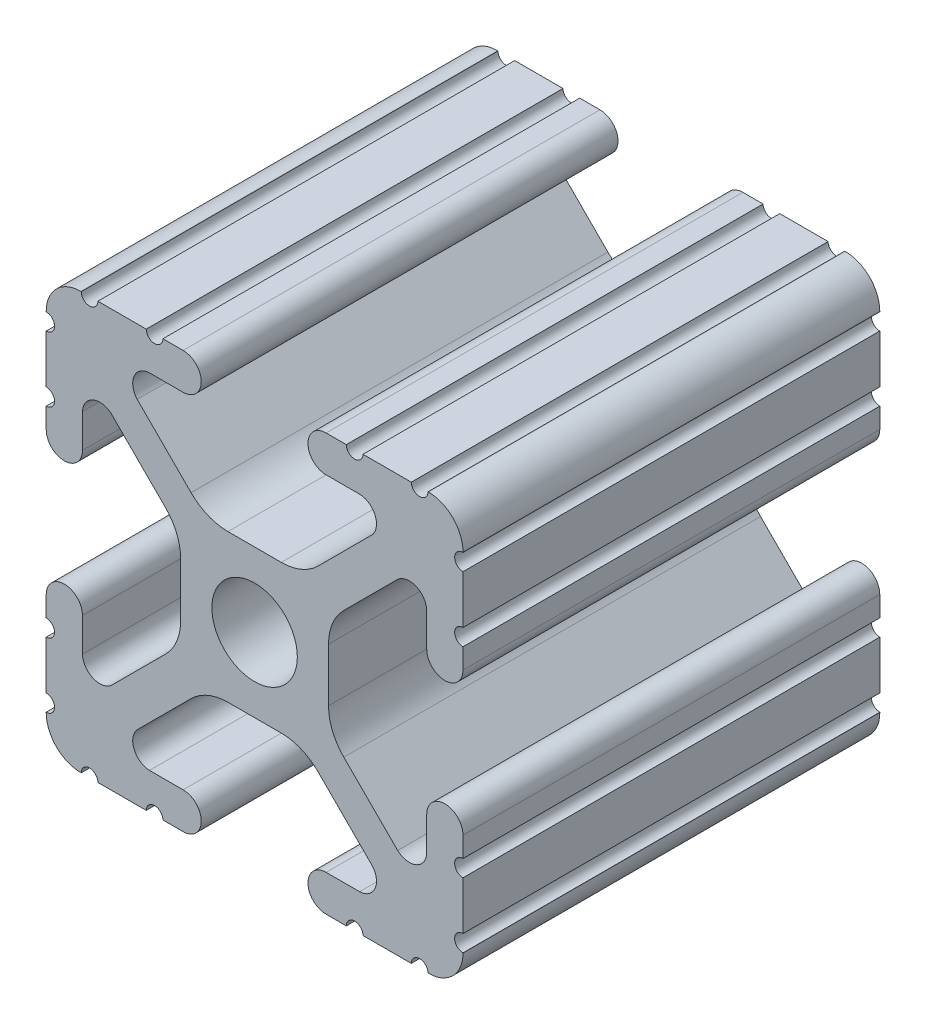
SolidWorks part; units mm, degrees
ref_plane "Front Plane" through (0, 0, 0) normal (0, 0, 1) x (1, 0, 0)
ref_plane "Top Plane" through (0, 0, 0) normal (0, 1, 0) x (1, 0, 0)
ref_plane "Right Plane" through (0, 0, 0) normal (1, 0, 0) x (0, 0, -1)
sketch "Sketch1" plane through (0, 0, 0) normal (0, 0, 1) x (1, 0, 0)
  line L0 (813.039, 579.2904) -> (813.039, 582.2368)
  line L1 (813.039, 583.2528) -> (813.039, 584.4847)
  line L2 (810.8292, 584.4847) -> (810.8292, 582.4359)
  line L3 (809.0573, 581.6856) -> (805.7733, 584.9696)
  line L4 (804.8434, 587.2147) -> (804.8434, 590.4671)
  line L5 (805.7733, 592.7122) -> (809.0571, 595.9959)
  line L6 (810.8292, 595.2394) -> (810.8292, 593.1969)
  line L7 (813.039, 593.1969) -> (813.039, 594.4288)
  line L8 (813.039, 595.4448) -> (813.039, 598.3912)
  line L9 (813.039, 599.4072) -> (813.039, 599.4326)
  line L10 (810.9308, 601.5408) -> (810.9054, 601.5408)
  line L11 (809.8894, 601.5408) -> (806.943, 601.5408)
  line L12 (805.927, 601.5408) -> (804.6951, 601.5408)
  line L13 (804.6951, 599.331) -> (806.7439, 599.331)
  line L14 (807.4942, 597.5592) -> (804.2102, 594.2752)
  line L15 (801.9651, 593.3452) -> (798.7127, 593.3452)
  line L16 (796.4676, 594.2752) -> (793.1839, 597.559)
  line L17 (793.9404, 599.331) -> (795.9829, 599.331)
  line L18 (795.9829, 601.5408) -> (794.751, 601.5408)
  line L19 (793.735, 601.5408) -> (790.7886, 601.5408)
  line L20 (789.7726, 601.5408) -> (789.7472, 601.5408)
  line L21 (787.639, 599.4326) -> (787.639, 599.4072)
  line L22 (787.639, 598.3912) -> (787.639, 595.4448)
  line L23 (787.639, 594.4288) -> (787.639, 593.1969)
  line L24 (789.8488, 593.1969) -> (789.8488, 595.2458)
  line L25 (791.6206, 595.996) -> (794.9046, 592.7121)
  line L26 (795.8346, 590.467) -> (795.8346, 587.2146)
  line L27 (794.9046, 584.9695) -> (791.6208, 581.6858)
  line L28 (789.8488, 582.4423) -> (789.8488, 584.4847)
  line L29 (787.639, 584.4847) -> (787.639, 583.2528)
  line L30 (787.639, 582.2368) -> (787.639, 579.2904)
  line L31 (787.639, 578.2744) -> (787.639, 578.249)
  line L32 (789.7472, 576.1408) -> (789.7726, 576.1408)
  line L33 (790.7886, 576.1408) -> (793.735, 576.1408)
  line L34 (794.751, 576.1408) -> (795.9829, 576.1408)
  line L35 (795.9829, 578.3506) -> (793.934, 578.3506)
  line L36 (793.1838, 580.1225) -> (796.4677, 583.4065)
  line L37 (798.7128, 584.3364) -> (801.9652, 584.3364)
  line L38 (804.2103, 583.4065) -> (807.494, 580.1227)
  line L39 (806.7375, 578.3506) -> (804.6951, 578.3506)
  line L40 (804.6951, 576.1408) -> (805.927, 576.1408)
  line L41 (806.943, 576.1408) -> (809.8894, 576.1408)
  line L42 (810.9054, 576.1408) -> (810.9308, 576.1408)
  line L43 (813.039, 578.249) -> (813.039, 578.2744)
  circle A0 centre (800.339, 588.8408) radius 2.6035
  arc A1 (813.039, 579.2904) -> (813.039, 578.2744) centre (813.039, 578.7824) ccw
  arc A2 (813.039, 583.2528) -> (813.039, 582.2368) centre (813.039, 582.7448) ccw
  arc A3 (813.039, 584.4847) -> (810.8292, 584.4847) centre (811.9341, 584.4847) ccw
  arc A4 (809.0573, 581.6856) -> (810.8292, 582.4359) centre (809.7692, 582.4718) ccw
  arc A5 (804.8434, 587.2147) -> (805.7733, 584.9696) centre (808.0184, 587.2147) ccw
  arc A6 (805.7733, 592.7122) -> (804.8434, 590.4671) centre (808.0184, 590.4671) ccw
  arc A7 (810.8292, 595.2394) -> (809.0571, 595.9959) centre (809.769, 595.2098) ccw
  arc A8 (810.8292, 593.1969) -> (813.039, 593.1969) centre (811.9341, 593.1969) ccw
  arc A9 (813.039, 595.4448) -> (813.039, 594.4288) centre (813.039, 594.9368) ccw
  arc A10 (813.039, 599.4072) -> (813.039, 598.3912) centre (813.039, 598.8992) ccw
  arc A11 (813.039, 599.4326) -> (810.9308, 601.5408) centre (810.9308, 599.4326) ccw
  arc A12 (809.8894, 601.5408) -> (810.9054, 601.5408) centre (810.3974, 601.5408) ccw
  arc A13 (805.927, 601.5408) -> (806.943, 601.5408) centre (806.435, 601.5408) ccw
  arc A14 (804.6951, 601.5408) -> (804.6951, 599.331) centre (804.6951, 600.4359) ccw
  arc A15 (807.4942, 597.5592) -> (806.7439, 599.331) centre (806.708, 598.2711) ccw
  arc A16 (801.9651, 593.3452) -> (804.2102, 594.2752) centre (801.9651, 596.5202) ccw
  arc A17 (796.4676, 594.2752) -> (798.7127, 593.3452) centre (798.7127, 596.5202) ccw
  arc A18 (793.9404, 599.331) -> (793.1839, 597.559) centre (793.97, 598.2709) ccw
  arc A19 (795.9829, 599.331) -> (795.9829, 601.5408) centre (795.9829, 600.4359) ccw
  arc A20 (793.735, 601.5408) -> (794.751, 601.5408) centre (794.243, 601.5408) ccw
  arc A21 (789.7726, 601.5408) -> (790.7886, 601.5408) centre (790.2806, 601.5408) ccw
  arc A22 (789.7472, 601.5408) -> (787.639, 599.4326) centre (789.7472, 599.4326) ccw
  arc A23 (787.639, 598.3912) -> (787.639, 599.4072) centre (787.639, 598.8992) ccw
  arc A24 (787.639, 594.4288) -> (787.639, 595.4448) centre (787.639, 594.9368) ccw
  arc A25 (787.639, 593.1969) -> (789.8488, 593.1969) centre (788.7439, 593.1969) ccw
  arc A26 (791.6206, 595.996) -> (789.8488, 595.2458) centre (790.9087, 595.2099) ccw
  arc A27 (795.8346, 590.467) -> (794.9046, 592.7121) centre (792.6596, 590.467) ccw
  arc A28 (794.9046, 584.9695) -> (795.8346, 587.2146) centre (792.6596, 587.2146) ccw
  arc A29 (789.8488, 582.4423) -> (791.6208, 581.6858) centre (790.9089, 582.4719) ccw
  arc A30 (789.8488, 584.4847) -> (787.639, 584.4847) centre (788.7439, 584.4847) ccw
  arc A31 (787.639, 582.2368) -> (787.639, 583.2528) centre (787.639, 582.7448) ccw
  arc A32 (787.639, 578.2744) -> (787.639, 579.2904) centre (787.639, 578.7824) ccw
  arc A33 (787.639, 578.249) -> (789.7472, 576.1408) centre (789.7472, 578.249) ccw
  arc A34 (790.7886, 576.1408) -> (789.7726, 576.1408) centre (790.2806, 576.1408) ccw
  arc A35 (794.751, 576.1408) -> (793.735, 576.1408) centre (794.243, 576.1408) ccw
  arc A36 (795.9829, 576.1408) -> (795.9829, 578.3506) centre (795.9829, 577.2457) ccw
  arc A37 (793.1838, 580.1225) -> (793.934, 578.3506) centre (793.9699, 579.4106) ccw
  arc A38 (798.7128, 584.3364) -> (796.4677, 583.4065) centre (798.7128, 581.1614) ccw
  arc A39 (804.2103, 583.4065) -> (801.9652, 584.3364) centre (801.9652, 581.1614) ccw
  arc A40 (806.7375, 578.3506) -> (807.494, 580.1227) centre (806.7079, 579.4108) ccw
  arc A41 (804.6951, 578.3506) -> (804.6951, 576.1408) centre (804.6951, 577.2457) ccw
  arc A42 (806.943, 576.1408) -> (805.927, 576.1408) centre (806.435, 576.1408) ccw
  arc A43 (810.9054, 576.1408) -> (809.8894, 576.1408) centre (810.3974, 576.1408) ccw
  arc A44 (810.9308, 576.1408) -> (813.039, 578.249) centre (810.9308, 578.249) ccw
extrude "Extrude1" add sketch "Sketch1" against normal blind 25.4
ref_plane "Plane1" through (806.943, 601.5408, -25.4) normal (0, 0, 1) x (1, 0, 0)
